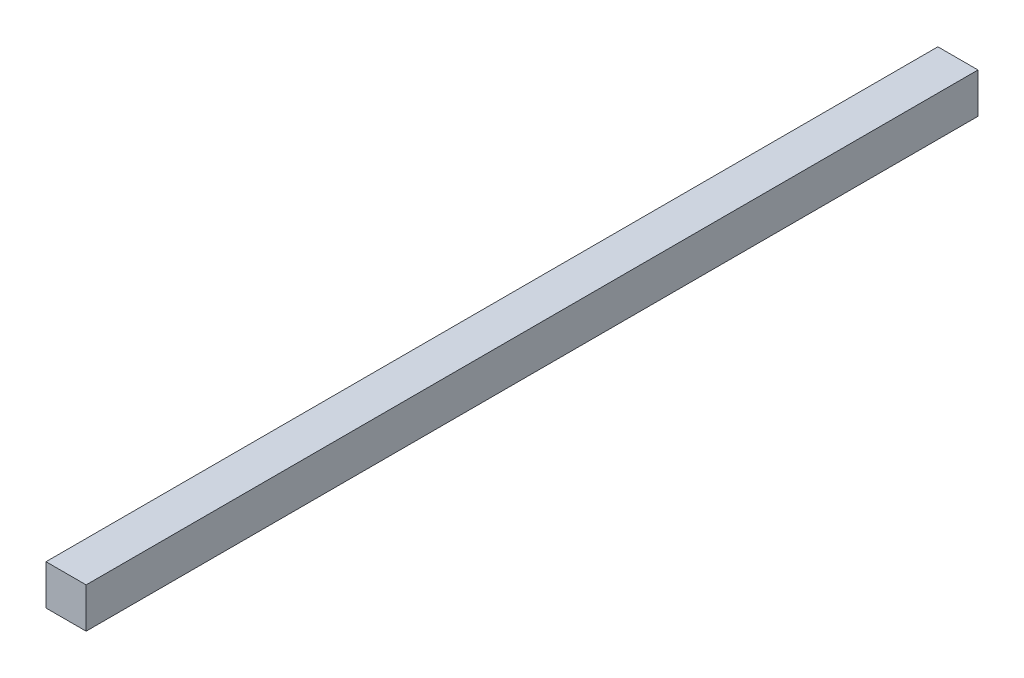
SolidWorks part; units mm, degrees
ref_plane "Front Plane" through (0, 0, 0) normal (0, 0, 1) x (1, 0, 0)
ref_plane "Top Plane" through (0, 0, 0) normal (0, 1, 0) x (1, 0, 0)
ref_plane "Right Plane" through (0, 0, 0) normal (1, 0, 0) x (0, 0, -1)
sketch "Sketch1" plane through (0, 0, 0) normal (0, 0, 1) x (1, 0, 0)
  line L1 (0, 0) -> (45, 0)
  line L2 (0, 0) -> (0, 45)
  line L3 (0, 45) -> (45, 45)
  line L4 (45, 0) -> (45, 45)
  dimension "D1" = 45
  dimension "D2" = 45
extrude "Boss-Extrude1" add sketch "Sketch1" along normal blind 1000
